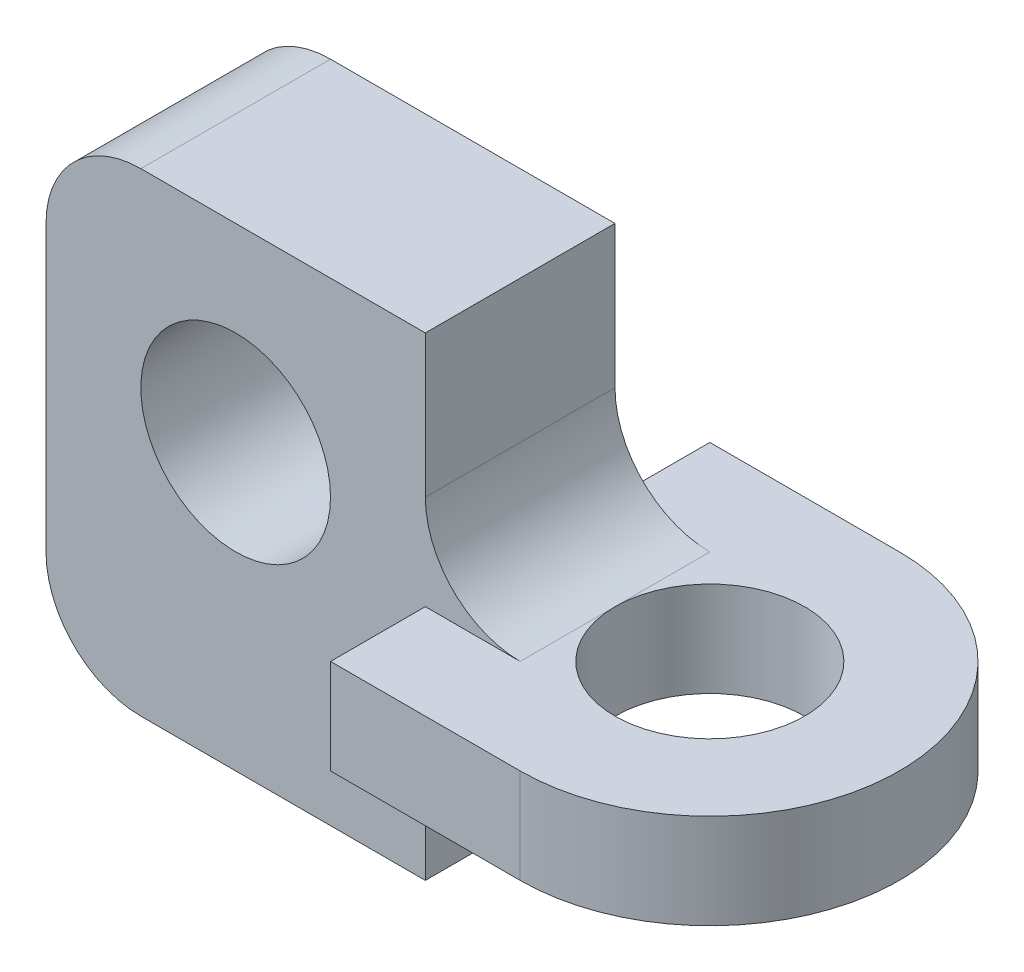
SolidWorks part; units mm, degrees
ref_plane "前基準面" through (0, 0, 0) normal (0, 0, 1) x (1, 0, 0)
ref_plane "上基準面" through (0, 0, 0) normal (0, 1, 0) x (1, 0, 0)
ref_plane "右基準面" through (0, 0, 0) normal (1, 0, 0) x (0, 0, -1)
sketch "草圖1" plane through (0, 0, 0) normal (0, 1, 0) x (1, 0, 0)
  line L0 (0, 10) -> (-10, 10)
  line L1 (-10, 10) -> (-10, -10)
  line L2 (-10, -10) -> (0, -10)
  circle A0 centre (0, 0) radius 5
  arc A1 (0, -10) -> (0, 10) centre (0, 0) ccw
  dimension "D1" = 20
  dimension "D2" = 10
extrude "填料-伸長1" add sketch "草圖1" along normal mid plane 5
sketch "草圖2" plane through (0, 0, 0) normal (0, 0, 1) x (1, 0, 0)
  line L0 (0, 0) -> (0, 5) construction
  line L1 (0, 5) -> (-20, 5) construction
  line L2 (-20, 5) -> (-20, -1.4071) construction
  line L3 (-30, 1.8983) -> (-30, -5)
  line L4 (-25, -10) -> (-10, -10)
  line L5 (-10, -10) -> (-10, -2.5)
  line L6 (-10, -2.5) -> (0, -2.5) construction
  line L7 (-30, 1.8983) -> (-30, 10)
  line L8 (-25, 15) -> (-10, 15)
  line L9 (-10, 15) -> (-10, 2.5)
  line L10 (-10, 2.5) -> (0, 2.5) construction
  line L11 (-10, 2.5) -> (-10, -2.5)
  circle A0 centre (-20, 5) radius 5
  arc A1 (-30, -5) -> (-25, -10) centre (-25, -5) ccw
  arc A2 (-30, 10) -> (-25, 15) centre (-25, 10) cw
  dimension "D3" = 10
  dimension "D4" = 10
  dimension "D7" = 5
  dimension "D1" = 5
  dimension "D2" = 20
  dimension "D5" = 10
  dimension "D6" = 15
extrude "填料-伸長2" add sketch "草圖2" along normal mid plane 10
fillet "圓角1" radius 5 2 edges at (-10, -2.5, 0) (-10, 2.5, 0)
